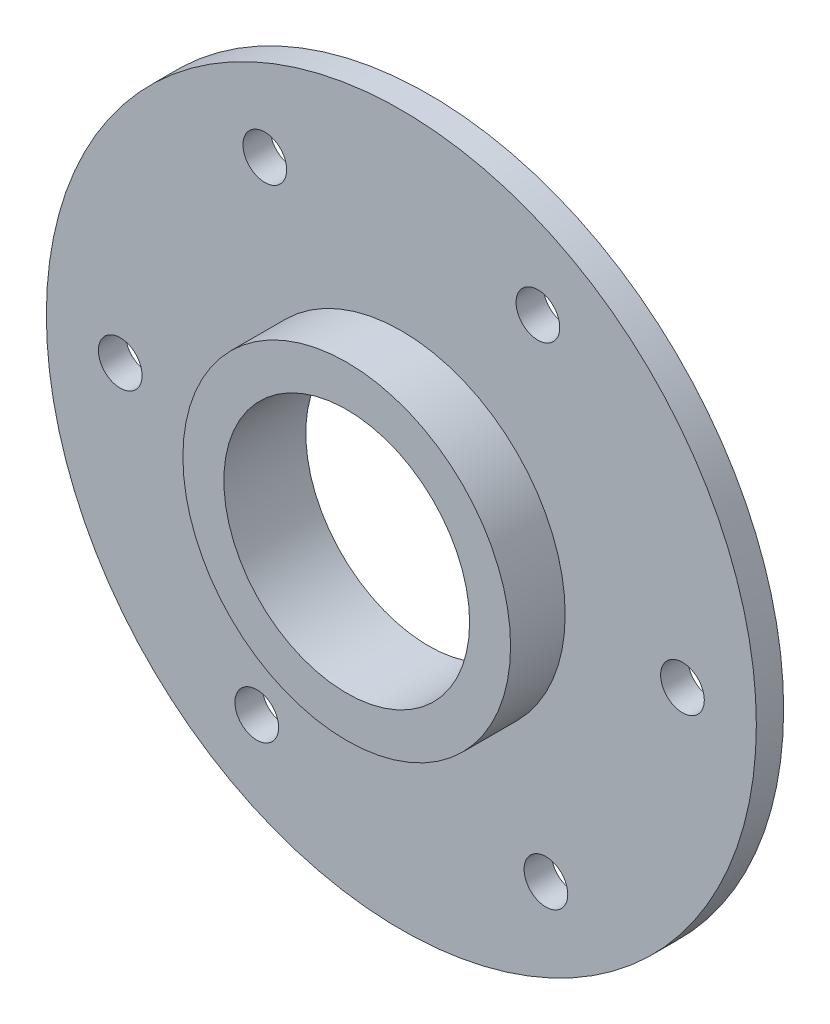
SolidWorks part; units mm, degrees
material "PF"
ref_plane "Front Plane" through (0, 0, 0) normal (0, 0, 1) x (1, 0, 0)
ref_plane "Top Plane" through (0, 0, 0) normal (0, 1, 0) x (1, 0, 0)
ref_plane "Right Plane" through (0, 0, 0) normal (1, 0, 0) x (0, 0, -1)
ref_plane "Plane1" through (0, 0, 5) normal (0, 0, 1) x (1, 0, 0)
sketch "Sketch1" plane through (0, 0, 5) normal (0, 0, 1) x (1, 0, 0)
  circle A0 centre (0, 0) radius 65
  dimension "D1" = 130
extrude "Boss-Extrude1" add sketch "Sketch1" against normal blind 5
sketch "Sketch11" plane through (0, 0, 5) normal (0, 0, 1) x (1, 0, 0)
  line L0 (-51.4711, -0.8494) -> (-26.4711, -44.1506) construction
  line L1 (-38.9711, -22.5) -> (0, 0) construction
  circle A3 centre (-25, 45) radius 4
  circle A4 centre (25, 45) radius 4
  circle A5 centre (26.4711, -44.1506) radius 4
  circle A6 centre (51.4711, -0.8494) radius 4
  circle A7 centre (-51.4711, -0.8494) radius 4
  circle A8 centre (-26.4711, -44.1506) radius 4
  point P11 (-3.1475, 0)
  point P20 (0, 0)
  dimension "D1" = 8
  dimension "D2" = 8
  dimension "D3" = 45
  dimension "D4" = 25
  dimension "D5" = 25
  dimension "D6" = 45
  dimension "D8" = 45
  dimension "D7" = 3
extrude "Cut-Extrude1" cut sketch "Sketch11" against normal blind 10
sketch "Sketch12" plane through (0, 0, 5) normal (0, 0, 1) x (1, 0, 0)
  circle A0 centre (0, 0) radius 30
  dimension "D2" = 60
extrude "Boss-Extrude2" add sketch "Sketch12" along normal blind 10
sketch "Sketch13" plane through (0, 0, 15) normal (0, 0, 1) x (1, 0, 0)
  circle A0 centre (0, 0) radius 22.5
  dimension "D1" = 45
extrude "Cut-Extrude2" cut sketch "Sketch13" against normal through all contours A0
